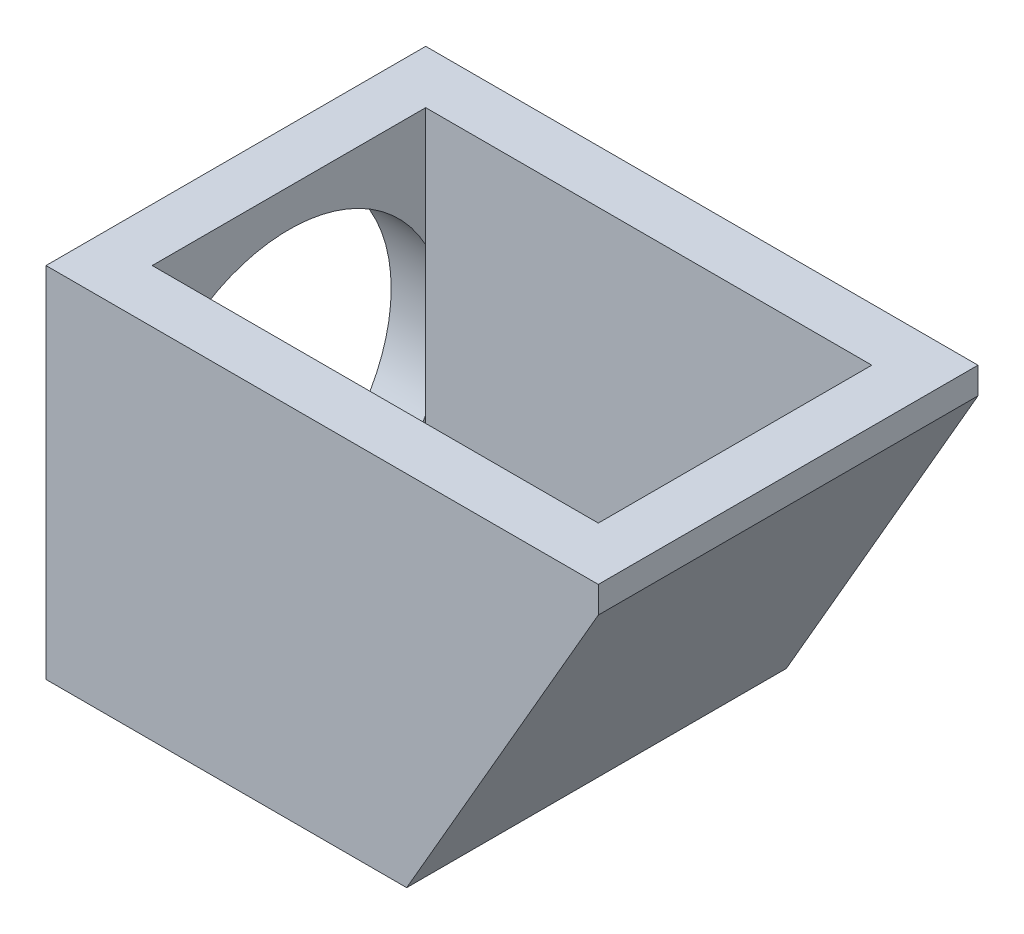
SolidWorks part; units mm, degrees
ref_plane "Front Plane" through (0, 0, 0) normal (0, 0, 1) x (1, 0, 0)
ref_plane "Top Plane" through (0, 0, 0) normal (0, 1, 0) x (1, 0, 0)
ref_plane "Right Plane" through (0, 0, 0) normal (1, 0, 0) x (0, 0, -1)
sketch "Sketch1" plane through (0, 0, 0) normal (0, 1, 0) x (1, 0, 0)
  line L0 (-10.4, 7.15) -> (10.4, 7.15)
  line L1 (-8.4, 5.15) -> (8.4, 5.15)
  line L2 (-8.4, 5.15) -> (-8.4, -5.15)
  line L3 (-8.4, -5.15) -> (8.4, -5.15)
  line L4 (8.4, 5.15) -> (8.4, -5.15)
  line L5 (-8.4, 5.15) -> (8.4, -5.15) construction
  line L6 (-8.4, -5.15) -> (8.4, 5.15) construction
  line L7 (10.4, 7.15) -> (10.4, -7.15)
  line L8 (-10.4, -7.15) -> (10.4, -7.15)
  line L9 (-10.4, 7.15) -> (-10.4, -7.15)
  point P0 (0, 0)
  dimension "D1" = 10.3
  dimension "D2" = 16.8
  dimension "D3" = 2
extrude "Boss-Extrude1" add sketch "Sketch1" along normal blind 12.5
sketch "Sketch2" plane through (0, 0, 0) normal (0, -1, 0) x (1, 0, 0)
  line L1 (-10.4, 7.15) -> (10.4, 7.15)
  line L2 (-10.4, 7.15) -> (-10.4, -7.15)
  line L3 (-10.4, -7.15) -> (10.4, -7.15)
  line L4 (10.4, 7.15) -> (10.4, -7.15)
extrude "Boss-Extrude2" add sketch "Sketch2" along normal blind 1
sketch "Sketch3" plane through (-10.4, 0, 0) normal (-1, 0, 0) x (0, 0, 1)
  circle A0 centre (0, 5.25) radius 5.25 construction
  circle A1 centre (0, 5.25) radius 5.85
  dimension "D1" = 10.5
  dimension "D2" = 11.7
extrude "Cut-Extrude2" cut sketch "Sketch3" against normal up to surface (2 mm away) up to face at (-8.4, 6.25, 0)
sketch "Sketch4" plane through (0, 0, 0) normal (0, 0, 1) x (1, 0, 0)
  line L0 (8.4, 11.5) -> (1.7605, 0)
  line L1 (8.4, 12.5) -> (8.4, 0) construction
  line L2 (8.4, 0) -> (-8.4, 0) construction
  line L3 (1.7605, 0) -> (8.4, 0)
  line L4 (8.4, 0) -> (8.4, 11.5)
  dimension "D1" = 1
  dimension "D2" = 60
extrude "Boss-Extrude3" add sketch "Sketch4" along normal mid plane 12
sketch "Sketch5" plane through (0, 0, 7.15) normal (0, 0, 1) x (1, 0, 0)
  line L0 (10.4, -1) -> (10.4, 11.5)
  line L1 (10.4, 12.5) -> (10.4, -1) construction
  line L2 (10.4, 11.5) -> (3.1831, -1)
  line L3 (10.4, -1) -> (-10.4, -1) construction
  line L4 (3.1831, -1) -> (10.4, -1)
  dimension "D1" = 1
  dimension "D2" = 60
extrude "Cut-Extrude3" cut sketch "Sketch5" against normal up to surface (14.3 mm away) up to face at (0, 5.75, -7.15)
